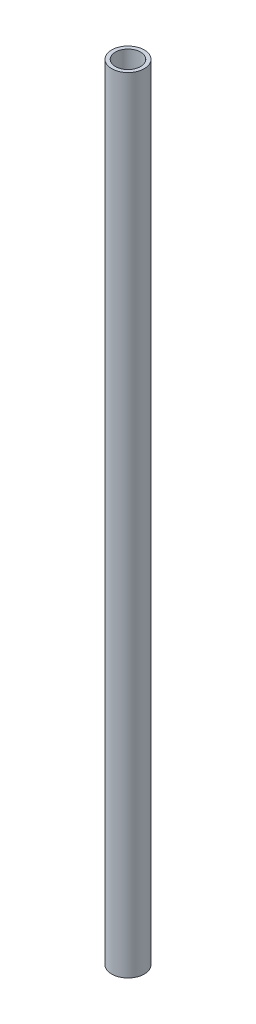
SolidWorks part; units mm, degrees
ref_plane "Front Plane" through (0, 0, 0) normal (0, 0, 1) x (1, 0, 0)
ref_plane "Top Plane" through (0, 0, 0) normal (0, 1, 0) x (1, 0, 0)
ref_plane "Right Plane" through (0, 0, 0) normal (1, 0, 0) x (0, 0, -1)
sketch "Sketch2" plane through (0, 0, 0) normal (0, 1, 0) x (1, 0, 0)
  circle A0 centre (0, 0) radius 4.6
  circle A1 centre (0, 0) radius 5.95
  dimension "D1" = 9.2
  dimension "D2" = 11.9
extrude "Boss-Extrude1" add sketch "Sketch2" along normal blind 286.5
